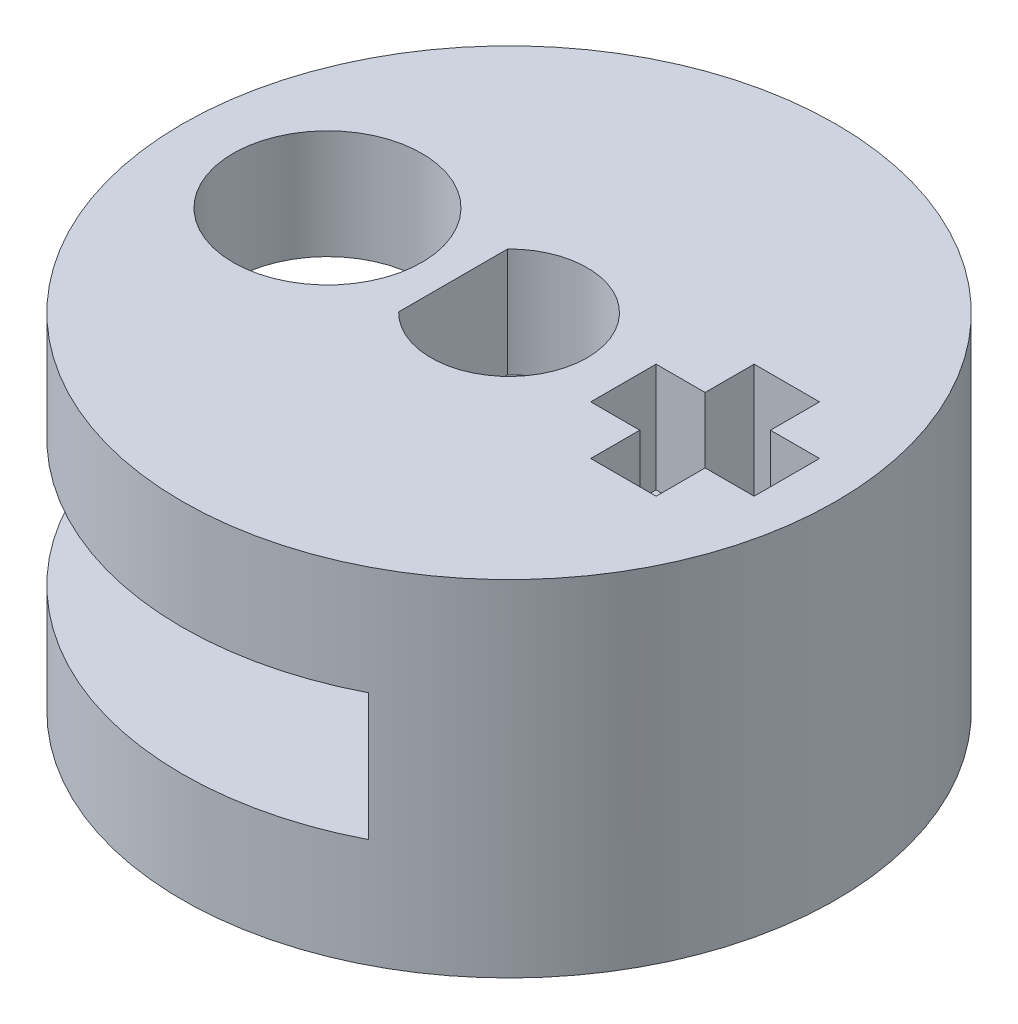
SolidWorks part; units mm, degrees
ref_plane "Front Plane" through (0, 0, 0) normal (0, 0, 1) x (1, 0, 0)
ref_plane "Top Plane" through (0, 0, 0) normal (0, 1, 0) x (1, 0, 0)
ref_plane "Right Plane" through (0, 0, 0) normal (1, 0, 0) x (0, 0, -1)
sketch "Sketch1" plane through (0, 0, 0) normal (0, 1, 0) x (1, 0, 0)
  line L14 (-1.5403, 1.5) -> (-1.5403, -1.5)
  circle A0 centre (0, 0) radius 9
  circle A3 centre (-5, 0) radius 2.6
  arc A4 (-1.5403, -1.5) -> (-1.5403, 1.5) centre (0, 0) ccw
  dimension "D1" = 18
  dimension "D3" = 5.2
  dimension "D15" = 4.3
  dimension "D2" = 5
  dimension "D16" = 3
extrude "Boss-Extrude1" add sketch "Sketch1" along normal blind 3
sketch "Sketch2" plane through (0, 0, 0) normal (0, -1, 0) x (1, 0, 0)
  line L0 (4.1231, 8) -> (4.1231, -8)
  circle A0 centre (0, 0) radius 9 construction
  arc A2 (4.1231, -8) -> (4.1231, 8) centre (0, 0) ccw
  dimension "D1" = 16
extrude "Boss-Extrude2" add sketch "Sketch2" along normal blind 3.5
sketch "Sketch4" plane through (0, -3.5, 0) normal (0, -1, 0) x (1, 0, 0)
  line L1 (4.1231, -8) -> (4.1231, 8)
  line L3 (4.1231, 8) -> (4.1231, -8)
  circle A0 centre (-5, 0) radius 2.6 construction
  arc A1 (4.1231, 8) -> (4.1231, -8) centre (0, 0) ccw
  arc A2 (4.1231, 8) -> (4.1231, -8) centre (0, 0) ccw
  arc A3 (4.1231, -8) -> (4.1231, 8) centre (0, 0) ccw
  arc A4 (4.1231, -8) -> (4.1231, 8) centre (0, 0) ccw
  circle A5 centre (-5, 0) radius 2.6
  dimension "D1" = 0
  dimension "D2" = 0
extrude "Boss-Extrude3" add sketch "Sketch4" along normal blind 3
sketch "Sketch5" plane through (0, 3, 0) normal (0, 1, 0) x (1, 0, 0)
  line L1 (3.25, 0.7984) -> (3.25, -1.0016)
  line L2 (3.25, -1.0016) -> (4.6, -1.0016)
  line L3 (4.6, -1.0016) -> (4.6, -2.3516)
  line L4 (4.6, -2.3516) -> (6.4, -2.3516)
  line L5 (6.4, -2.3516) -> (6.4, -1.0016)
  line L6 (6.4, -1.0016) -> (7.75, -1.0016)
  line L7 (7.75, -1.0016) -> (7.75, 0.7984)
  line L8 (7.75, 0.7984) -> (6.4, 0.7984)
  line L9 (6.4, 0.7984) -> (6.4, 2.1484)
  line L10 (6.4, 2.1484) -> (4.6, 2.1484)
  line L11 (4.6, 2.1484) -> (4.6, 0.7984)
  line L12 (4.6, 0.7984) -> (3.25, 0.7984)
  line L13 (-1.5403, 1.5) -> (-1.5403, -1.5) construction
  line L14 (-1.5403, 1.5) -> (-1.5403, -1.5)
  circle A0 centre (-5, 0) radius 2.5
  circle A3 centre (5.5, -0.1016) radius 2.4233 construction
  arc A5 (-1.5403, -1.5) -> (-1.5403, 1.5) centre (0, 0) ccw construction
  circle A8 centre (0, 0) radius 9.1
  arc A9 (-1.5403, -1.5) -> (-1.5403, 1.5) centre (0, 0) ccw
  dimension "D2" = 1.8
  dimension "D1" = 1.35
extrude "Cut-Extrude1" cut sketch "Sketch5" against normal blind 10 contours L1 L2 L3 L4 L5 L6 L7 L8 L9 L10 L11 L12
sketch "Sketch6" plane through (0, -6.5, 0) normal (0, -1, 0) x (1, 0, 0)
  line L1 (7.75, 1.0016) -> (6.4, 1.0016) construction
  line L2 (7.75, 1.0016) -> (6.4, 1.0016)
  line L3 (4.6, 2.3516) -> (4.6, 1.0016) construction
  line L4 (6.4, 2.3516) -> (4.6, 2.3516) construction
  line L5 (6.4, 1.0016) -> (6.4, 2.3516) construction
  line L6 (4.6, 1.0016) -> (3.25, 1.0016) construction
  line L7 (3.25, 1.0016) -> (3.25, -0.7984) construction
  line L8 (3.25, -0.7984) -> (4.6, -0.7984) construction
  line L9 (4.6, -0.7984) -> (4.6, -2.1484) construction
  line L10 (4.6, -2.1484) -> (6.4, -2.1484) construction
  line L11 (6.4, -2.1484) -> (6.4, -0.7984) construction
  line L12 (6.4, -0.7984) -> (7.75, -0.7984) construction
  line L13 (7.75, -0.7984) -> (7.75, 1.0016) construction
  line L14 (4.6, -2.1484) -> (6.4, -2.1484)
  line L15 (6.4, -2.1484) -> (6.4, -0.7984)
  line L16 (6.4, -0.7984) -> (7.75, -0.7984)
  line L17 (7.75, -0.7984) -> (7.75, 1.0016)
  line L18 (4.6, -0.7984) -> (4.6, -2.1484)
  line L19 (3.25, -0.7984) -> (4.6, -0.7984)
  line L20 (3.25, 1.0016) -> (3.25, -0.7984)
  line L21 (4.6, 1.0016) -> (3.25, 1.0016)
  line L22 (6.4, 1.0016) -> (6.4, 2.3516)
  line L23 (6.4, 2.3516) -> (4.6, 2.3516)
  line L24 (4.6, 2.3516) -> (4.6, 1.0016)
  circle A2 centre (-5, 0) radius 2.5
  circle A7 centre (0, 0) radius 9.1
